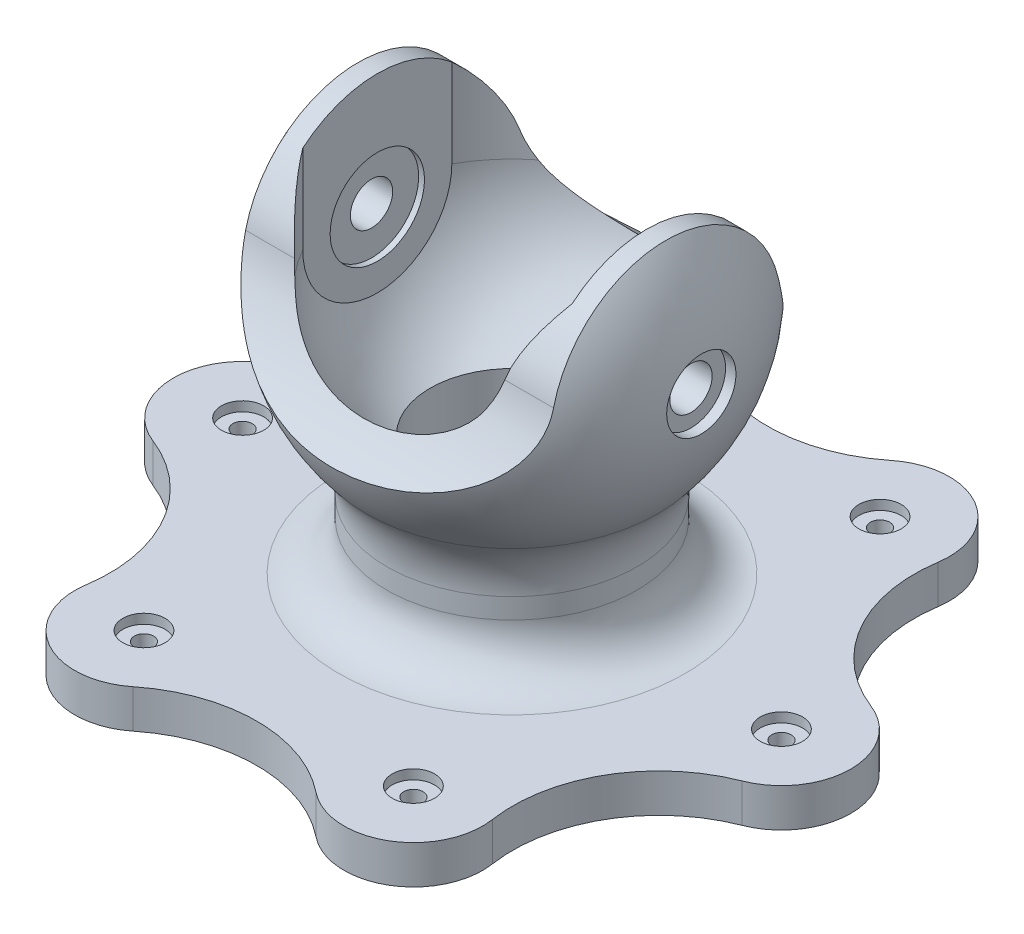
SolidWorks part; units mm, degrees
material "1060 Alloy"
ref_plane "Front Plane" through (0, 0, 0) normal (0, 0, 1) x (1, 0, 0)
ref_plane "Top Plane" through (0, 0, 0) normal (0, 1, 0) x (1, 0, 0)
ref_plane "Right Plane" through (0, 0, 0) normal (1, 0, 0) x (0, 0, -1)
sketch "Sketch1" plane through (0, 0, 0) normal (0, 0, 1) x (1, 0, 0)
  line L0 (0, 150) -> (0, 0) construction
  line L1 (0, 0) -> (60, 0) construction
  line L2 (0, 0) -> (60, 0)
  line L3 (60, 0) -> (60, -6)
  line L4 (60, -6) -> (76, -6)
  line L5 (76, -6) -> (76, 0)
  line L6 (76, 0) -> (176, 0)
  line L7 (176, 0) -> (176, 20)
  line L8 (176, 20) -> (65, 20)
  line L9 (65, 20) -> (65, 74.0066)
  line L10 (0, 0) -> (0, 250)
  arc A0 (65, 74.0066) -> (0, 250) centre (0, 150) ccw
  point P15 (76, -3)
  dimension "D7" = 100
  dimension "D1" = 352
  dimension "D2" = 120
  dimension "D3" = 152
  dimension "D4" = 20
  dimension "D5" = 6
  dimension "D6" = 130
  dimension "D8" = 150
revolve "Revolve1" add sketch "Sketch1" angle 360 about L10
fillet "Fillet2" radius 25 1 edges at (65, 20, 0)
fillet "Fillet3" radius 45 1 edges at (65, 74.0066, 0)
sketch "Sketch2" plane through (0, 0, 0) normal (1, 0, 0) x (0, 0, -1)
  line L0 (0, 0) -> (0, 250) construction
  line L1 (0, 0) -> (32, 0)
  line L2 (-76, 0) -> (76, 0) construction
  line L3 (32, 0) -> (32, 49)
  line L4 (32, 49) -> (42.5, 49)
  line L5 (42.5, 49) -> (42.5, 82.2228)
  line L6 (80, 150) -> (80, 250)
  line L7 (80, 250) -> (0, 250)
  line L8 (0, 0) -> (0, 250)
  arc A0 (75.8621, 84.8467) -> (-75.8621, 84.8467) centre (0, 150) ccw construction
  arc A1 (42.5, 82.2228) -> (80, 150) centre (0, 150) ccw
  dimension "D2" = 85
  dimension "D5" = 80
  dimension "D1" = 64
  dimension "D3" = 49
  dimension "D4" = 150
revolve "Cut-Revolve1" cut sketch "Sketch2" angle 360 about L0
sketch "Sketch3" plane through (0, 0, 0) normal (1, 0, 0) x (0, 0, -1)
  line L0 (0, 150) -> (0, 0) construction
  line L1 (80, 210) -> (-80, 210) construction
  line L2 (80, 210) -> (-80, 210)
  arc A1 (58.4116, 163.7143) -> (-58.4116, 163.7143) centre (0, 150) ccw
  arc A2 (-93.461, 114.4326) -> (-58.4116, 163.7143) centre (-136.2938, 182) ccw
  arc A3 (93.461, 114.4326) -> (58.4116, 163.7143) centre (136.2938, 182) cw
  arc A4 (75.8621, 84.8467) -> (80, 210) centre (0, 150) ccw construction
  arc A5 (-80, 210) -> (-75.8621, 84.8467) centre (0, 150) ccw construction
  arc A6 (75.8621, 84.8467) -> (80, 210) centre (0, 150) ccw
  arc A7 (-80, 210) -> (-93.461, 114.4326) centre (0, 150) ccw
  dimension "D2" = 120
  dimension "D3" = 160
  dimension "D4" = 182
extrude "Cut-Extrude1" cut sketch "Sketch3" against normal through all both and the other way through all contours A3 A6 L2 A1 | L2 A7 A2 A1
ref_plane "Plane1" through (70, 0, 0) normal (1, 0, 0) x (0, 0, -1)
sketch "Sketch4" plane through (70, 0, 0) normal (1, 0, 0) x (0, 0, -1)
  line L0 (-38.7298, 195.8258) -> (-38.7298, 150)
  line L1 (38.7298, 150) -> (38.7298, 195.8258)
  line L2 (38.7298, 150) -> (38.7298, 195.8258)
  line L3 (-38.7298, 195.8258) -> (-38.7298, 150)
  arc A0 (-38.7298, 150) -> (38.7298, 150) centre (0, 150) ccw
  arc A1 (-38.7298, 150) -> (38.7298, 150) centre (0, 150) ccw
  arc A2 (58.4116, 163.7143) -> (0, 210) centre (0, 150) ccw construction
  arc A3 (0, 210) -> (-58.4116, 163.7143) centre (0, 150) ccw construction
  arc A4 (38.7298, 195.8258) -> (0, 210) centre (0, 150) ccw
  arc A5 (0, 210) -> (-38.7298, 195.8258) centre (0, 150) ccw
extrude "Boss-Extrude1" add sketch "Sketch4" along normal up to surface
sketch "Sketch5" plane through (0, 0, 0) normal (0, 0, 1) x (1, 0, 0)
  line L0 (0, 0) -> (0, 150) construction
  line L1 (0, 150) -> (100, 150) construction
  line L2 (100, 150) -> (100, 168)
  line L3 (100, 168) -> (93, 168)
  line L4 (93, 168) -> (93, 161)
  line L5 (93, 161) -> (73, 161)
  line L6 (73, 161) -> (73, 174.5)
  line L7 (73, 174.5) -> (70, 174.5)
  line L8 (70, 174.5) -> (70, 150)
  line L9 (100, 150) -> (70, 150)
  arc A1 (75.8621, 84.8467) -> (80, 210) centre (0, 150) ccw construction
  point P3 (71.5, 174.5)
  dimension "D1" = 150
  dimension "D2" = 49
  dimension "D3" = 22
  dimension "D4" = 36
  dimension "D5" = 70
  dimension "D6" = 73
  dimension "D7" = 93
revolve "Cut-Revolve2" cut sketch "Sketch5" angle 360 about L1
mirror "Mirror1" about plane through (0, 0, 0) normal (1, 0, 0) of "Cut-Revolve2", "Boss-Extrude1"
sketch "Sketch6" plane through (0, 20, 0) normal (0, 1, 0) x (1, 0, 0)
  line L0 (0, 0) -> (140, 0) construction
  line L1 (0, 0) -> (52, 90.0666) construction
  arc A4 (105.5875, 115.8092) -> (153.0875, 33.5368) centre (180.7166, 104.3368) ccw
  arc A5 (88, 152.4205) -> (176, 0) centre (0, 0) cw
  circle A7 centre (0, 0) radius 176 construction
  arc A8 (36.7676, 135.0857) -> (70, 121.2436) centre (0, 0) ccw construction
  arc A9 (105.5875, 115.8092) -> (88, 152.4205) centre (70, 121.2436) ccw
  arc A10 (176, 0) -> (153.0875, 33.5368) centre (140, 0) ccw
  dimension "D1" = 280
  dimension "D2" = 72
  dimension "D4" = 76
  dimension "D3" = 60
extrude "Cut-Extrude3" cut sketch "Sketch6" against normal through all contours A10 A4 A9 A5
pattern_circular "CirPattern1" count 6 over 360 about axis through (0, 0, 0) along (0, 1, 0) of "Cut-Extrude3"
sketch "Sketch7" plane through (0, 0, 0) normal (0, 0, 1) x (1, 0, 0)
  line L0 (140, 20) -> (140, 0) construction
  line L1 (153.0875, 20) -> (104.7166, 20) construction
  line L2 (104.7166, 0) -> (153.0875, 0) construction
  line L3 (140, 0) -> (157.5, 0)
  line L4 (157.5, 0) -> (157.5, 2)
  line L5 (157.5, 2) -> (145, 2)
  line L6 (145, 2) -> (145, 15)
  line L7 (145, 15) -> (151, 15)
  line L8 (151, 15) -> (151, 20)
  line L9 (151, 20) -> (140, 20)
  line L10 (140, 20) -> (140, 0)
  dimension "D1" = 22
  dimension "D2" = 10
  dimension "D3" = 35
  dimension "D4" = 140
  dimension "D5" = 5
  dimension "D6" = 2
revolve "Cut-Revolve3" cut sketch "Sketch7" angle 360 about L0
pattern_circular "CirPattern2" count 6 over 360 about axis through (0, 0, 0) along (0, 1, 0) of "Cut-Revolve3"
chamfer "Chamfer1" distance 1.5 angle 45 1 edges at (76, -6, 0)
